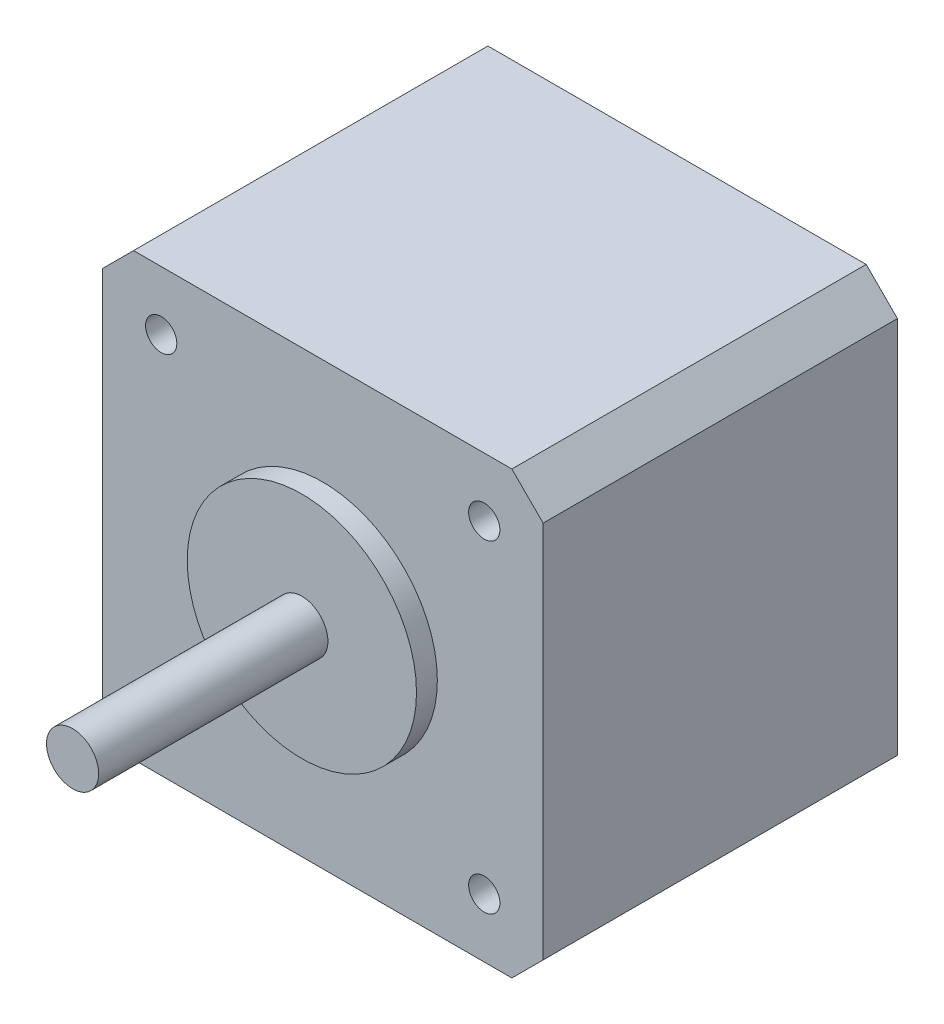
SolidWorks part; units mm, degrees
ref_plane "前视基准面" through (0, 0, 0) normal (0, 0, 1) x (1, 0, 0)
ref_plane "上视基准面" through (0, 0, 0) normal (0, 1, 0) x (1, 0, 0)
ref_plane "右视基准面" through (0, 0, 0) normal (1, 0, 0) x (0, 0, -1)
ref_plane "基准面4" through (0, 0, 29) normal (0, 0, 1) x (1, 0, 0)
sketch "草图1" plane through (0, 0, 29) normal (0, 0, 1) x (1, 0, 0)
  line L0 (58.85, -21.15) -> (101.15, -21.15)
  line L1 (101.15, -21.15) -> (101.15, 21.15)
  line L2 (101.15, 21.15) -> (58.85, 21.15)
  line L3 (58.85, 21.15) -> (58.85, -21.15)
extrude "凸台-拉伸1" add sketch "草图1" against normal blind 34
ref_plane "基准面5" through (0, 0, 0) normal (0, -1, 0) x (1, 0, 0)
sketch "草图2" plane through (0, 0, 0) normal (0, -1, 0) x (1, 0, 0)
  line L0 (82.5, 53) -> (80, 53)
  line L1 (80, 53) -> (80, 29)
  line L2 (80, 29) -> (91, 29)
  line L3 (91, 29) -> (91, 31)
  line L4 (91, 31) -> (82.5, 31)
  line L5 (82.5, 31) -> (82.5, 53)
  line L6 (80, 53) -> (80, 29) construction
revolve "旋转1" add sketch "草图2" angle 360 about L6
hole_wizard "Ø3.0 (3) 直径孔1" positions "草图4" profile "草图3" hole size "Ø3.0" standard "ANSI Metric"
sketch "草图4" plane through (0, 0, 29) normal (0, 0, 1) x (1, 0, 0)
  point P0 (95.5, 15.5)
  point P1 (95.5, -15.5)
  point P2 (64.5, -15.5)
  point P3 (64.5, 15.5)
sketch "草图3" plane through (95.5, 15.5, 29) normal (1, 0, 0) x (0, -1, 0)
  line L0 (0, 0) -> (0, 5)
  line L1 (0, 5) -> (1.5, 5)
  line L2 (1.5, 5) -> (1.5, 0)
  line L5 (1.5, 0) -> (0, 0)
  line L10 (0, 5) -> (-1.5, 5) construction
  line L11 (0, -6.35) -> (0, 107.95) construction
  dimension "孔直径" = 3
  dimension "孔深度" = 5
  dimension "导头角度" = 180
chamfer "倒角1" distance 3 angle 45 4 edges at (58.85, 21.15, 12) (58.85, -21.15, 12) (101.15, 21.15, 12) (101.15, -21.15, 12)
